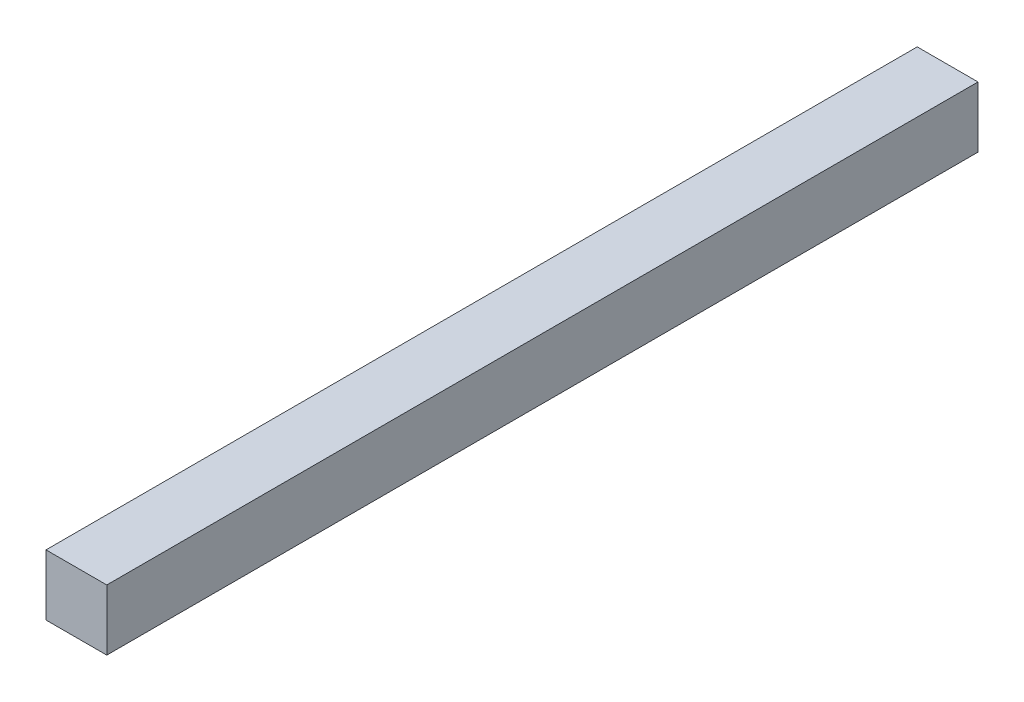
SolidWorks part; units mm, degrees
ref_plane "Face" through (0, 0, 0) normal (0, 0, 1) x (1, 0, 0)
ref_plane "Dessus" through (0, 0, 0) normal (0, 1, 0) x (1, 0, 0)
ref_plane "Droite" through (0, 0, 0) normal (1, 0, 0) x (0, 0, -1)
sketch "Esquisse1" plane through (0, 0, 0) normal (0, 0, 1) x (1, 0, 0)
  line L1 (0, 0) -> (18, 0)
  line L2 (0, 0) -> (0, 18)
  line L3 (0, 18) -> (18, 18)
  line L4 (18, 0) -> (18, 18)
  dimension "D1" = 18
  dimension "D2" = 18
extrude "Extrusion1" add sketch "Esquisse1" against normal blind 258
